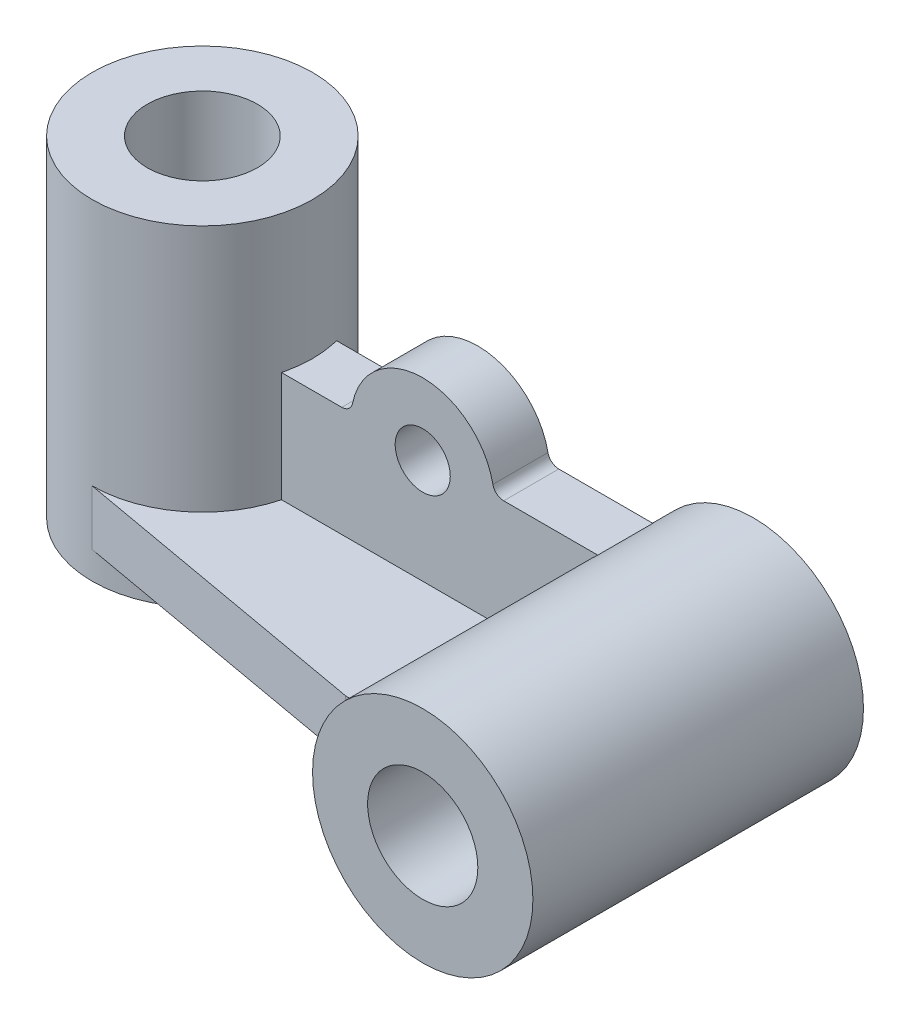
SolidWorks part; units mm, degrees
ref_plane "Front Plane" through (0, 0, 0) normal (0, 0, 1) x (1, 0, 0)
ref_plane "Top Plane" through (0, 0, 0) normal (0, 1, 0) x (1, 0, 0)
ref_plane "Right Plane" through (0, 0, 0) normal (1, 0, 0) x (0, 0, -1)
sketch "Sketch1" plane through (0, 0, 0) normal (0, 0, 1) x (1, 0, 0)
  line L0 (0, 44.4281) -> (0, -80.0714) construction
  line L1 (-28.6057, 0) -> (38.9394, 0) construction
  line L2 (0, 30) -> (0, -30)
  line L3 (0, -30) -> (20, -30)
  line L4 (20, -30) -> (20, 30)
  line L5 (20, 30) -> (0, 30)
  line L6 (10, 30) -> (10, -30)
  dimension "D1" = 60
  dimension "big-cyl-purple" = 20
  dimension "small-cyl-purple" = 10
revolve "cyl- purple" add sketch "Sketch1" angle 360 about L2
ref_plane "Plane2" through (0, 0, 50) normal (0, 0, 1) x (1, 0, 0)
sketch "Sketch3" plane through (0, 0, 50) normal (0, 0, 1) x (1, 0, 0)
  line L0 (-41.145, 0) -> (181.0552, 0) construction
  line L1 (0, 53.1866) -> (0, -50.2505) construction
  line L2 (90, 47.9131) -> (90, -59.9766) construction
  line L3 (0, -30) -> (191.1627, -30) construction
  circle A0 centre (90, -10) radius 20
  circle A1 centre (90, -10) radius 10
  dimension "big-cyl-blue" = 40
  dimension "small-cyl-blue" = 20
  dimension "D3" = 90
  dimension "D4" = 30
  dimension "D5" = 20
extrude "cyl- blue" add sketch "Sketch3" against normal blind 60 separate body
ref_plane "Plane3" through (0, 0, -5) normal (0, 0, 1) x (1, 0, 0)
sketch "Sketch4" plane through (0, 0, -5) normal (0, 0, 1) x (1, 0, 0)
  line L0 (-19.6228, -30) -> (145.0037, -30) construction
  line L1 (-20, -30) -> (20, -30) construction
  line L2 (0, 39.5007) -> (0, -49.1941) construction
  line L4 (-38.69, -15) -> (133.7763, -15) construction
  line L5 (10, -15) -> (70.6351, -15)
  line L6 (10, 5) -> (30.3031, 5)
  line L8 (10, 5) -> (10, -15)
  line L9 (59.6969, 5) -> (76.7712, 5)
  circle A0 centre (90, -10) radius 20 construction
  arc A1 (70.6351, -15) -> (76.7712, 5) centre (90, -10) cw
  circle A4 centre (90, -10) radius 10 construction
  arc A7 (32.2627, 6.6) -> (57.7373, 6.6) centre (45, 4) cw
  circle A8 centre (45, 4) radius 5
  arc A9 (59.6969, 5) -> (57.7373, 6.6) centre (59.6969, 7) cw
  arc A10 (30.3031, 5) -> (32.2627, 6.6) centre (30.3031, 7) ccw
  dimension "D2" = 13
  dimension "D3" = 10
  dimension "D4" = 45
  dimension "D5" = 2
  dimension "D8" = 10
  dimension "D9" = 19
  dimension "D1" = 20
  dimension "D6" = 15
  dimension "D7" = 20
extrude "base- yellow" add sketch "Sketch4" along normal blind 10 separate body
ref_plane "Plane4" through (0, -25, 0) normal (0, 1, 0) x (1, 0, 0)
sketch "Sketch6" plane through (0, -25, 0) normal (0, 1, 0) x (1, 0, 0)
  line L0 (0, 35.6481) -> (0, 20) construction
  line L1 (-44.6641, 0) -> (126.7478, 0) construction
  line L8 (0, 0) -> (0, -43.6764) construction
  line L13 (110, -50) -> (110, -74.8178) construction
  line L14 (0, -20) -> (56, -30)
  line L17 (10, -5) -> (70.6351, -5) construction
  line L19 (19.3649, -5) -> (77.3091, -5)
  line L21 (56, -30) -> (77.3091, -30)
  line L22 (77.3091, -30) -> (77.3091, -5)
  circle A2 centre (0, 0) radius 20 construction
  arc A3 (0, -20) -> (19.3649, -5) centre (0, 0) ccw
  point P6 (70, -30)
  dimension "D1" = 25
  dimension "D2" = 56
  dimension "D3" = 14
  dimension "D4" = 77.3091
extrude "base-red" add sketch "Sketch6" along normal blind 10 separate body
equation "\"small-cyl-purple@Sketch1\"=\"big-cyl-purple@Sketch1\"/2"
equation "\"small-cyl-blue@Sketch3\"=\"big-cyl-blue@Sketch3\"/2"
